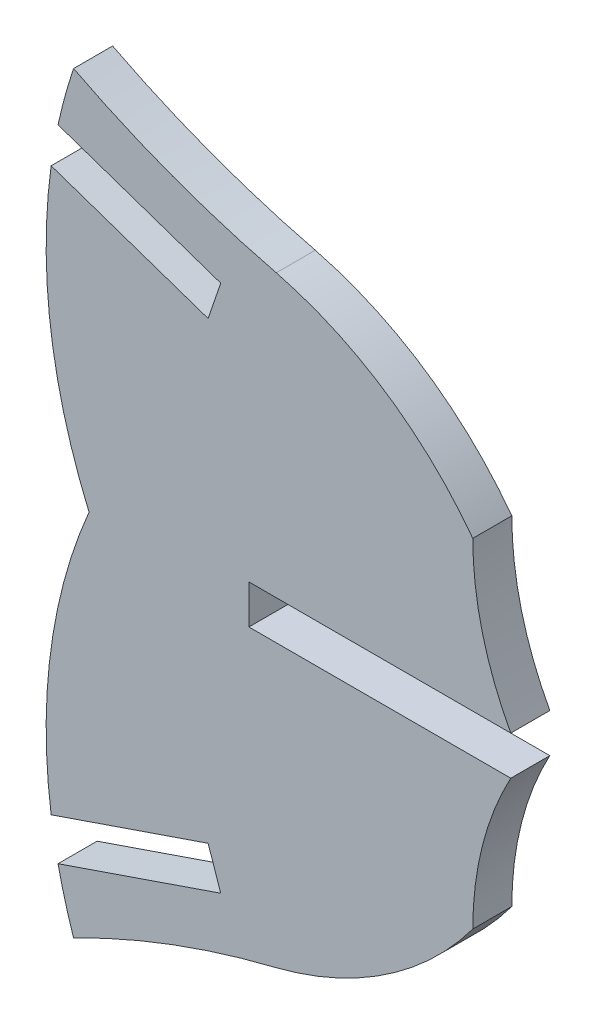
SolidWorks part; units mm, degrees
ref_plane "Front Plane" through (0, 0, 0) normal (0, 0, 1) x (1, 0, 0)
ref_plane "Top Plane" through (0, 0, 0) normal (0, 1, 0) x (1, 0, 0)
ref_plane "Right Plane" through (0, 0, 0) normal (1, 0, 0) x (0, 0, -1)
sketch "Sketch1" plane through (0, 0, 0) normal (0, 0, 1) x (1, 0, 0)
  line L0 (0.2854, 0) -> (0.2854, -1.524)
  line L1 (0.2854, -1.524) -> (10.5084, -1.524)
  line L2 (-5.955, -1.524) -> (-5.955, 0) construction
  line L3 (-5.955, -0.762) -> (-12.5641, -0.762) construction
  line L4 (-0.8135, 9.5507) -> (-1.3077, 8.109)
  line L5 (-7.1652, -13.2516) -> (-0.8135, -11.0747)
  line L6 (-7.4341, -11.7328) -> (-1.3077, -9.633)
  line L7 (-7.4341, 10.2088) -> (-1.3077, 8.109)
  line L8 (-0.8135, -11.0747) -> (-1.3077, -9.633)
  line L9 (-7.1652, 11.7276) -> (-0.8135, 9.5507)
  line L10 (0.2854, 0) -> (10.5084, 0)
  arc A0 (10.5084, -1.524) -> (9.0246, -7.3662) centre (21.2674, -7.3662) ccw
  arc A1 (-6.5592, 13.9329) -> (1.3537, 10.9854) centre (9.964, 46.1957) ccw
  arc A2 (1.3537, -12.5094) -> (9.0246, -7.3662) centre (-2.0459, 0.853) ccw
  arc A3 (-6.5592, -15.4569) -> (-7.1652, -13.2516) centre (12.9854, -8.9007) cw
  arc A4 (-7.4341, -11.7328) -> (-5.955, -0.762) centre (12.9854, -8.9007) cw
  arc A5 (-7.4341, 10.2088) -> (-5.955, -0.762) centre (12.9854, 7.3767) ccw
  arc A6 (-6.5592, 13.9329) -> (-7.1652, 11.7276) centre (12.9854, 7.3767) ccw
  arc A7 (1.3537, 10.9854) -> (9.0246, 5.8422) centre (-2.0459, -2.377) cw
  arc A9 (10.5084, 0) -> (9.0246, 5.8422) centre (21.2674, 5.8422) cw
  arc A10 (-6.5592, -15.4569) -> (1.3537, -12.5094) centre (9.964, -47.7197) cw
  point P20 (-7.5605, -11.7761)
extrude "Boss-Extrude1" add sketch "Sketch1" along normal blind 1.524
